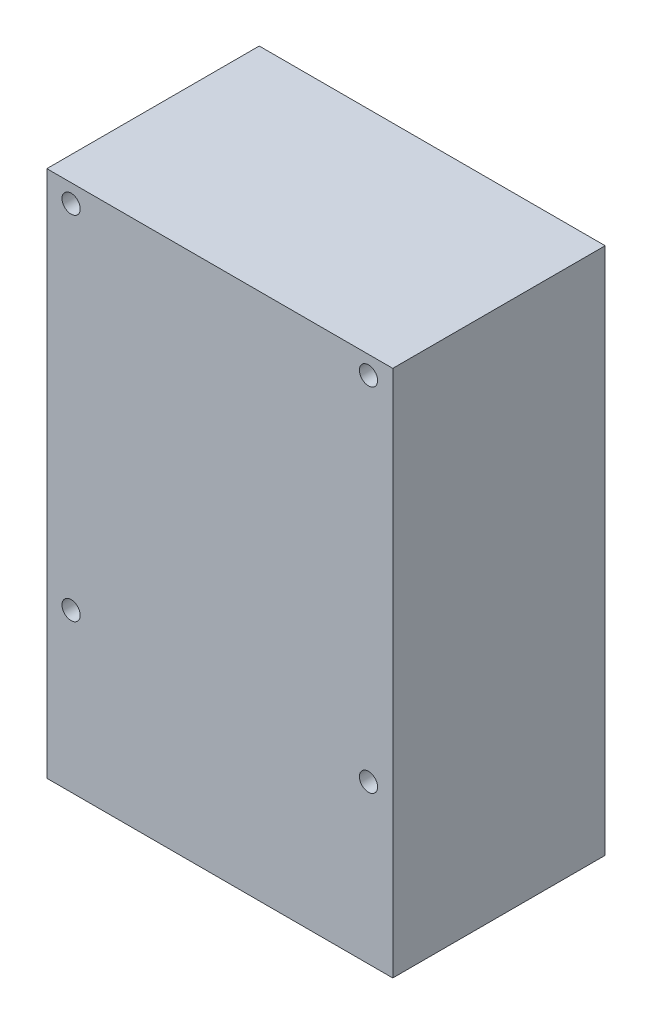
SolidWorks part; units mm, degrees
ref_plane "Front Plane" through (0, 0, 0) normal (0, 0, 1) x (1, 0, 0)
ref_plane "Top Plane" through (0, 0, 0) normal (0, 1, 0) x (1, 0, 0)
ref_plane "Right Plane" through (0, 0, 0) normal (1, 0, 0) x (0, 0, -1)
sketch "Sketch1" plane through (0, 0, 0) normal (0, 0, 1) x (1, 0, 0)
  line L1 (28.5, 43.5) -> (-28.5, 43.5)
  line L2 (28.5, 43.5) -> (28.5, -43.5)
  line L3 (28.5, -43.5) -> (-28.5, -43.5)
  line L4 (-28.5, 43.5) -> (-28.5, -43.5)
  line L5 (28.5, 43.5) -> (-28.5, -43.5) construction
  line L6 (28.5, -43.5) -> (-28.5, 43.5) construction
  point P0 (0, 0)
  dimension "D1" = 87
  dimension "D2" = 57
extrude "Boss-Extrude1" add sketch "Sketch1" along normal blind 35
sketch "Sketch2" plane through (0, 0, 0) normal (0, 0, -1) x (-1, 0, 0)
  line L0 (-24.5, 40.5) -> (24.5, 40.5) construction
  line L1 (-28.5, 43.5) -> (28.5, 43.5) construction
  circle A0 centre (-24.5, 40.5) radius 1.5
  circle A1 centre (24.5, 40.5) radius 1.5
  circle A2 centre (-24.5, -17.5) radius 1.5
  circle A3 centre (24.5, -17.5) radius 1.5
  point P8 (0, 40.5)
  dimension "D1" = 3
  dimension "D2" = 3
  dimension "D3" = 49
  dimension "D4" = 58
extrude "Cut-Extrude1" cut sketch "Sketch2" against normal through all
